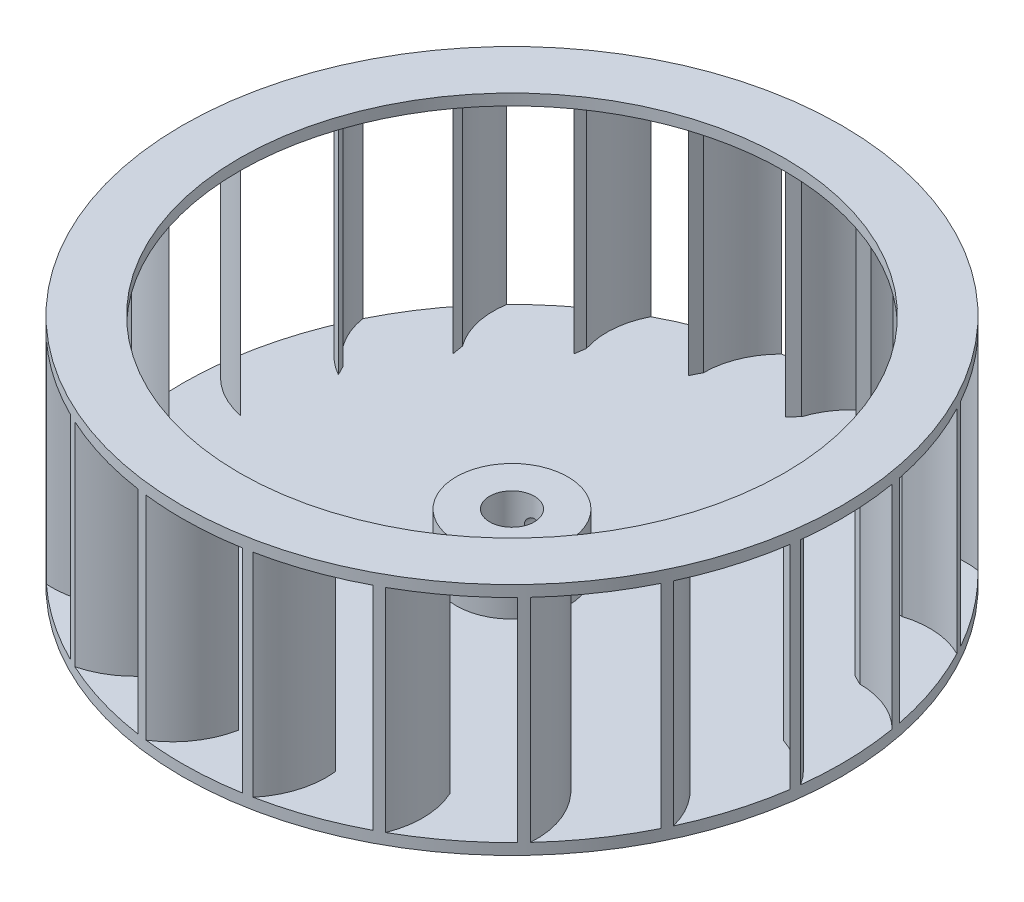
SolidWorks part; units mm, degrees
material "1060 Alloy"
ref_plane "Front Plane" through (0, 0, 0) normal (0, 0, 1) x (1, 0, 0)
ref_plane "Top Plane" through (0, 0, 0) normal (0, 1, 0) x (1, 0, 0)
ref_plane "Right Plane" through (0, 0, 0) normal (1, 0, 0) x (0, 0, -1)
sketch "Sketch2" plane through (0, 0, 0) normal (0, 1, 0) x (1, 0, 0)
  circle A0 centre (0, 0) radius 59
  dimension "D1" = 118
extrude "Boss-Extrude1" add sketch "Sketch2" along normal blind 2
sketch "Sketch3" plane through (0, 2, 0) normal (0, 1, 0) x (1, 0, 0)
  line L0 (-14.8929, 46.4744) -> (-14, 48.2641)
  line L1 (0, 48.2641) -> (0, 0) construction
  line L2 (-9.8995, 58.1636) -> (0, 48.2641) construction
  line L3 (0, 48.2641) -> (-33.9349, 48.2641) construction
  line L4 (0.1974, 48.802) -> (1.5996, 50.2281)
  line L5 (15.2684, 46.3524) -> (17.0427, 47.2754)
  line L6 (28.8448, 39.3656) -> (30.8175, 39.6951)
  line L7 (39.5977, 28.5253) -> (41.5756, 28.2292)
  line L8 (46.4744, 14.8929) -> (48.2641, 14)
  line L9 (48.802, -0.1974) -> (50.2281, -1.5996)
  line L10 (46.3524, -15.2684) -> (47.2754, -17.0427)
  line L11 (39.3656, -28.8448) -> (39.6951, -30.8175)
  line L12 (28.5253, -39.5977) -> (28.2292, -41.5756)
  line L13 (14.8929, -46.4744) -> (14, -48.2641)
  line L14 (-0.1974, -48.802) -> (-1.5996, -50.2281)
  line L15 (-15.2684, -46.3524) -> (-17.0427, -47.2754)
  line L16 (-28.8448, -39.3656) -> (-30.8175, -39.6951)
  line L17 (-39.5977, -28.5253) -> (-41.5756, -28.2292)
  line L18 (-46.4744, -14.8929) -> (-48.2641, -14)
  line L19 (-48.802, 0.1974) -> (-50.2281, 1.5996)
  line L20 (-46.3524, 15.2684) -> (-47.2754, 17.0427)
  line L21 (-39.3656, 28.8448) -> (-39.6951, 30.8175)
  line L22 (-28.5253, 39.5977) -> (-28.2292, 41.5756)
  arc A0 (-11.5264, 57.8631) -> (-14.8929, 46.4744) centre (0, 48.2641) ccw
  circle A1 centre (0, 0) radius 59 construction
  arc A2 (-9.8995, 58.1636) -> (-14, 48.2641) centre (0, 48.2641) ccw
  arc A3 (-11.5264, 57.8631) -> (-9.8995, 58.1636) centre (0, 0) cw
  arc A4 (6.9184, 58.593) -> (0.1974, 48.802) centre (14.9144, 45.9019) ccw
  arc A5 (8.5586, 58.3759) -> (1.5996, 50.2281) centre (14.9144, 45.9019) ccw
  arc A6 (6.9184, 58.593) -> (8.5586, 58.3759) centre (0, 0) cw
  arc A7 (24.686, 53.5873) -> (15.2684, 46.3524) centre (28.3689, 39.0465) ccw
  arc A8 (26.1788, 52.8741) -> (17.0427, 47.2754) centre (28.3689, 39.0465) ccw
  arc A9 (24.686, 53.5873) -> (26.1788, 52.8741) centre (0, 0) cw
  arc A10 (40.0372, 43.3362) -> (28.8448, 39.3656) centre (39.0465, 28.3689) ccw
  arc A11 (41.2365, 42.1965) -> (30.8175, 39.6951) centre (39.0465, 28.3689) ccw
  arc A12 (40.0372, 43.3362) -> (41.2365, 42.1965) centre (0, 0) cw
  arc A13 (51.4693, 28.843) -> (39.5977, 28.5253) centre (45.9019, 14.9144) ccw
  arc A14 (52.2577, 27.3885) -> (41.5756, 28.2292) centre (45.9019, 14.9144) ccw
  arc A15 (51.4693, 28.843) -> (52.2577, 27.3885) centre (0, 0) cw
  arc A16 (57.8631, 11.5264) -> (46.4744, 14.8929) centre (48.2641, 0) ccw
  arc A17 (58.1636, 9.8995) -> (48.2641, 14) centre (48.2641, 0) ccw
  arc A18 (57.8631, 11.5264) -> (58.1636, 9.8995) centre (0, 0) cw
  arc A19 (58.593, -6.9184) -> (48.802, -0.1974) centre (45.9019, -14.9144) ccw
  arc A20 (58.3759, -8.5586) -> (50.2281, -1.5996) centre (45.9019, -14.9144) ccw
  arc A21 (58.593, -6.9184) -> (58.3759, -8.5586) centre (0, 0) cw
  arc A22 (53.5873, -24.686) -> (46.3524, -15.2684) centre (39.0465, -28.3689) ccw
  arc A23 (52.8741, -26.1788) -> (47.2754, -17.0427) centre (39.0465, -28.3689) ccw
  arc A24 (53.5873, -24.686) -> (52.8741, -26.1788) centre (0, 0) cw
  arc A25 (43.3362, -40.0372) -> (39.3656, -28.8448) centre (28.3689, -39.0465) ccw
  arc A26 (42.1965, -41.2365) -> (39.6951, -30.8175) centre (28.3689, -39.0465) ccw
  arc A27 (43.3362, -40.0372) -> (42.1965, -41.2365) centre (0, 0) cw
  arc A28 (28.843, -51.4693) -> (28.5253, -39.5977) centre (14.9144, -45.9019) ccw
  arc A29 (27.3885, -52.2577) -> (28.2292, -41.5756) centre (14.9144, -45.9019) ccw
  arc A30 (28.843, -51.4693) -> (27.3885, -52.2577) centre (0, 0) cw
  arc A31 (11.5264, -57.8631) -> (14.8929, -46.4744) centre (0, -48.2641) ccw
  arc A32 (9.8995, -58.1636) -> (14, -48.2641) centre (0, -48.2641) ccw
  arc A33 (11.5264, -57.8631) -> (9.8995, -58.1636) centre (0, 0) cw
  arc A34 (-6.9184, -58.593) -> (-0.1974, -48.802) centre (-14.9144, -45.9019) ccw
  arc A35 (-8.5586, -58.3759) -> (-1.5996, -50.2281) centre (-14.9144, -45.9019) ccw
  arc A36 (-6.9184, -58.593) -> (-8.5586, -58.3759) centre (0, 0) cw
  arc A37 (-24.686, -53.5873) -> (-15.2684, -46.3524) centre (-28.3689, -39.0465) ccw
  arc A38 (-26.1788, -52.8741) -> (-17.0427, -47.2754) centre (-28.3689, -39.0465) ccw
  arc A39 (-24.686, -53.5873) -> (-26.1788, -52.8741) centre (0, 0) cw
  arc A40 (-40.0372, -43.3362) -> (-28.8448, -39.3656) centre (-39.0465, -28.3689) ccw
  arc A41 (-41.2365, -42.1965) -> (-30.8175, -39.6951) centre (-39.0465, -28.3689) ccw
  arc A42 (-40.0372, -43.3362) -> (-41.2365, -42.1965) centre (0, 0) cw
  arc A43 (-51.4693, -28.843) -> (-39.5977, -28.5253) centre (-45.9019, -14.9144) ccw
  arc A44 (-52.2577, -27.3885) -> (-41.5756, -28.2292) centre (-45.9019, -14.9144) ccw
  arc A45 (-51.4693, -28.843) -> (-52.2577, -27.3885) centre (0, 0) cw
  arc A46 (-57.8631, -11.5264) -> (-46.4744, -14.8929) centre (-48.2641, 0) ccw
  arc A47 (-58.1636, -9.8995) -> (-48.2641, -14) centre (-48.2641, 0) ccw
  arc A48 (-57.8631, -11.5264) -> (-58.1636, -9.8995) centre (0, 0) cw
  arc A49 (-58.593, 6.9184) -> (-48.802, 0.1974) centre (-45.9019, 14.9144) ccw
  arc A50 (-58.3759, 8.5586) -> (-50.2281, 1.5996) centre (-45.9019, 14.9144) ccw
  arc A51 (-58.593, 6.9184) -> (-58.3759, 8.5586) centre (0, 0) cw
  arc A52 (-53.5873, 24.686) -> (-46.3524, 15.2684) centre (-39.0465, 28.3689) ccw
  arc A53 (-52.8741, 26.1788) -> (-47.2754, 17.0427) centre (-39.0465, 28.3689) ccw
  arc A54 (-53.5873, 24.686) -> (-52.8741, 26.1788) centre (0, 0) cw
  arc A55 (-43.3362, 40.0372) -> (-39.3656, 28.8448) centre (-28.3689, 39.0465) ccw
  arc A56 (-42.1965, 41.2365) -> (-39.6951, 30.8175) centre (-28.3689, 39.0465) ccw
  arc A57 (-43.3362, 40.0372) -> (-42.1965, 41.2365) centre (0, 0) cw
  arc A58 (-28.843, 51.4693) -> (-28.5253, 39.5977) centre (-14.9144, 45.9019) ccw
  arc A59 (-27.3885, 52.2577) -> (-28.2292, 41.5756) centre (-14.9144, 45.9019) ccw
  arc A60 (-28.843, 51.4693) -> (-27.3885, 52.2577) centre (0, 0) cw
  dimension "D1" = 14
  dimension "D2" = 15
  dimension "D3" = 2
  dimension "D4" = 45
  dimension "D5" = 20
extrude "Boss-Extrude2" add sketch "Sketch3" along normal blind 38
sketch "Sketch4" plane through (0, 40, 0) normal (0, 1, 0) x (1, 0, 0)
  circle A0 centre (0, 0) radius 59
  circle A1 centre (0, 0) radius 48.8024
  circle A2 centre (0, 0) radius 59 construction
extrude "Boss-Extrude3" add sketch "Sketch4" along normal blind 2
sketch "Sketch5" plane through (0, 2, 0) normal (0, 1, 0) x (1, 0, 0)
  circle A0 centre (0, 0) radius 10
  circle A1 centre (0, 0) radius 4
  dimension "D1" = 8
  dimension "D2" = 20
extrude "Boss-Extrude4" add sketch "Sketch5" along normal blind 10
sketch "Sketch6" plane through (0, 0, 0) normal (0, 0, 1) x (1, 0, 0)
  line L0 (0, 12) -> (0, 2) construction
  line L1 (10, 12) -> (-10, 12) construction
  line L2 (9.8995, 2) -> (-6.9184, 2) construction
  circle A0 centre (0, 7) radius 1.5
  dimension "D1" = 3
extrude "Cut-Extrude1" cut sketch "Sketch6" against normal blind 25
sketch "Sketch7" plane through (0, 2, 0) normal (0, 1, 0) x (1, 0, 0)
  circle A1 centre (0, 0) radius 4
  circle A2 centre (0, 0) radius 4
  dimension "D1" = 0
extrude "Cut-Extrude2" cut sketch "Sketch7" against normal through all
